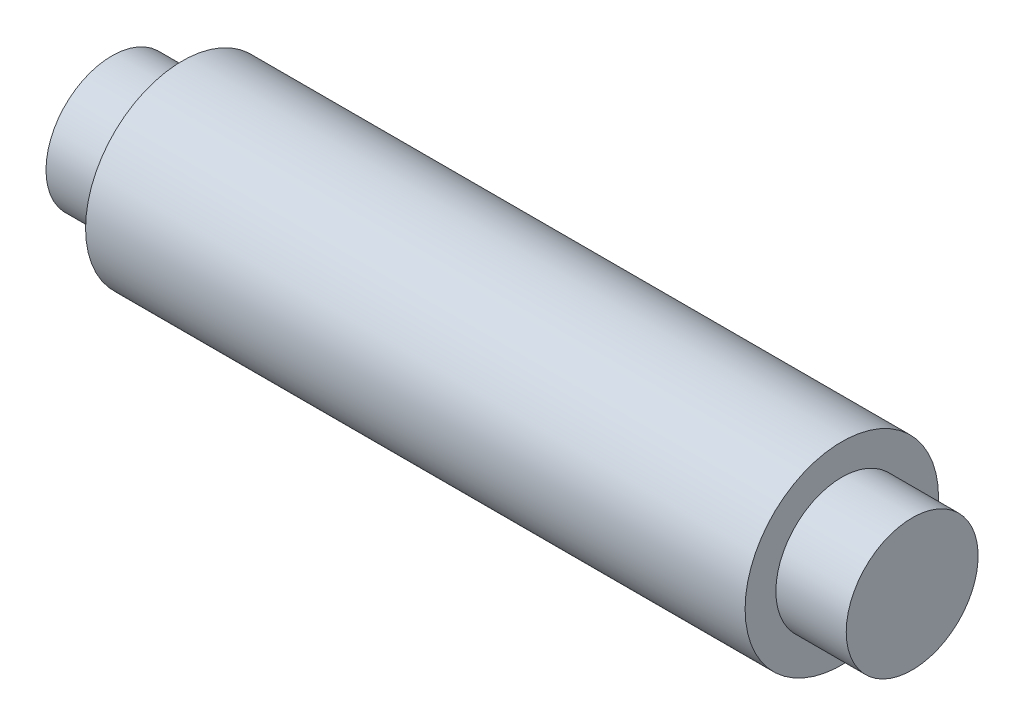
SolidWorks part; units mm, degrees
material "1.0037 (S235JR)"
ref_plane "Front Plane" through (0, 0, 0) normal (0, 0, 1) x (1, 0, 0)
ref_plane "Top Plane" through (0, 0, 0) normal (0, 1, 0) x (1, 0, 0)
ref_plane "Right Plane" through (0, 0, 0) normal (1, 0, 0) x (0, 0, -1)
sketch "Sketch1" plane through (0, 0, 0) normal (0, 0, 1) x (1, 0, 0)
  line L0 (-45.5, 0) -> (45.5, 0) construction
  line L1 (-45.5, 0) -> (-45.5, 7.5)
  line L2 (-45.5, 7.5) -> (-37.5, 7.5)
  line L3 (-37.5, 7.5) -> (-37.5, 11)
  line L4 (-37.5, 11) -> (37.5, 11)
  line L5 (37.5, 11) -> (37.5, 7.5)
  line L6 (37.5, 7.5) -> (45.5, 7.5)
  line L7 (45.5, 7.5) -> (45.5, 0)
  line L8 (0, 0) -> (0, 11) construction
  line L9 (-45.5, 0) -> (45.5, 0)
  dimension "D1" = 22
  dimension "D2" = 15
  dimension "D3" = 8
  dimension "D4" = 75
revolve "Revolve1" add sketch "Sketch1" angle 360 about L9
